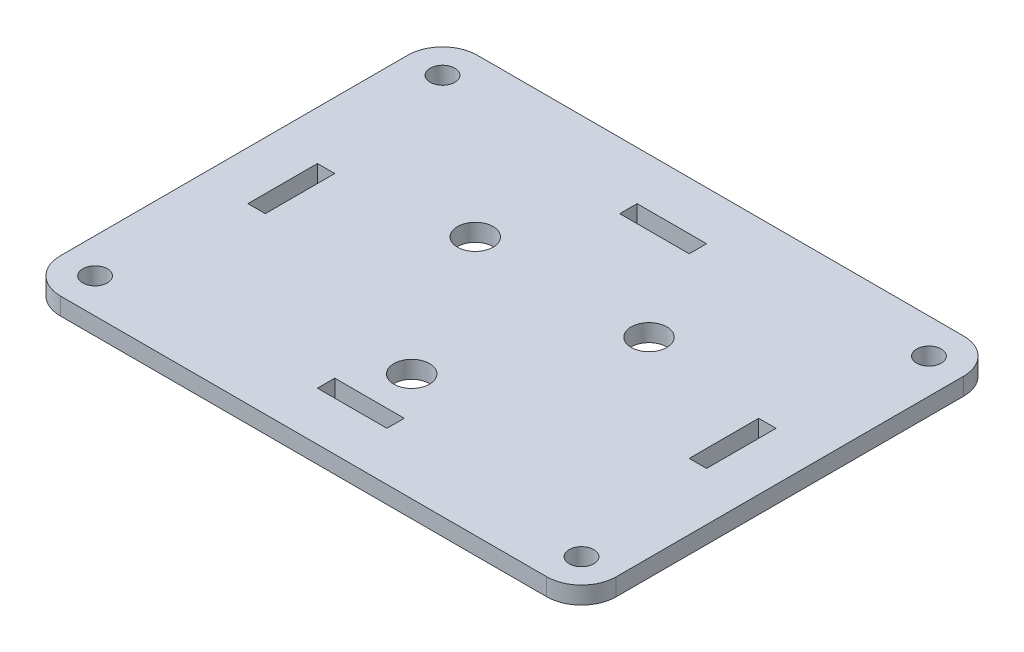
SolidWorks part; units mm, degrees
material "Acrylic (Medium-high impact)"
ref_plane "Front Plane" through (0, 0, 0) normal (0, 0, 1) x (1, 0, 0)
ref_plane "Top Plane" through (0, 0, 0) normal (0, 1, 0) x (1, 0, 0)
ref_plane "Right Plane" through (0, 0, 0) normal (1, 0, 0) x (0, 0, -1)
sketch "Sketch1" plane through (0, 0, 0) normal (0, 1, 0) x (1, 0, 0)
  line L1 (-50.8, -38.1) -> (50.8, -38.1)
  line L2 (-50.8, -38.1) -> (-50.8, 38.1)
  line L3 (-50.8, 38.1) -> (50.8, 38.1)
  line L4 (50.8, -38.1) -> (50.8, 38.1)
  line L5 (-50.8, -38.1) -> (50.8, 38.1) construction
  line L6 (-50.8, 38.1) -> (50.8, -38.1) construction
  point P0 (0, 0)
  dimension "D1" = 101.6
  dimension "D2" = 76.2
extrude "Boss-Extrude1" add sketch "Sketch1" along normal blind 3.175
fillet "Fillet1" radius 6.35 4 edges at (50.8, 1.5875, 38.1) (50.8, 1.5875, -38.1) (-50.8, 1.5875, -38.1) (-50.8, 1.5875, 38.1)
sketch "Sketch2" plane through (0, 3.175, 0) normal (0, 1, 0) x (1, 0, 0)
  line L0 (-50.8, 0) -> (-41.91, 0) construction
  line L1 (-50.8, 31.75) -> (-50.8, -31.75) construction
  line L2 (0, 38.1) -> (0, 29.21) construction
  line L3 (44.45, 38.1) -> (-44.45, 38.1) construction
  line L4 (50.8, 0) -> (41.91, 0) construction
  line L5 (50.8, -31.75) -> (50.8, 31.75) construction
  line L6 (0, -38.1) -> (0, -29.21) construction
  line L7 (-44.45, -38.1) -> (44.45, -38.1) construction
  line L8 (-41.91, 0) -> (-41.91, 6.35)
  line L9 (-41.91, 6.35) -> (-38.735, 6.35)
  line L10 (-38.735, 6.35) -> (-38.735, -6.35)
  line L11 (-38.735, -6.35) -> (-41.91, -6.35)
  line L12 (-41.91, -6.35) -> (-41.91, 0)
  line L13 (0, 29.21) -> (6.35, 29.21)
  line L14 (6.35, 29.21) -> (6.35, 26.035)
  line L15 (6.35, 26.035) -> (-6.35, 26.035)
  line L16 (-6.35, 26.035) -> (-6.35, 29.21)
  line L17 (-6.35, 29.21) -> (0, 29.21)
  line L18 (41.91, 0) -> (41.91, 6.35)
  line L19 (41.91, 6.35) -> (38.735, 6.35)
  line L20 (38.735, 6.35) -> (38.735, -6.35)
  line L21 (38.735, -6.35) -> (41.91, -6.35)
  line L22 (41.91, -6.35) -> (41.91, 0)
  line L23 (0, -29.21) -> (6.35, -29.21)
  line L24 (6.35, -29.21) -> (6.35, -26.035)
  line L25 (6.35, -26.035) -> (-6.35, -26.035)
  line L26 (-6.35, -26.035) -> (-6.35, -29.21)
  line L27 (-6.35, -29.21) -> (0, -29.21)
  circle A0 centre (-44.45, 31.75) radius 2.2479
  circle A1 centre (44.45, 31.75) radius 2.2479
  circle A2 centre (44.45, -31.75) radius 2.2479
  circle A3 centre (-44.45, -31.75) radius 2.2479
  dimension "D1" = 4.4958
  dimension "D2" = 8.89
  dimension "D3" = 3.175
  dimension "D4" = 8.89
  dimension "D5" = 3.175
  dimension "D6" = 12.7
  dimension "D7" = 12.7
extrude "Cut-Extrude1" cut sketch "Sketch2" against normal through all
sketch "Sketch3" plane through (0, 3.175, 0) normal (0, 1, 0) x (1, 0, 0)
  line L0 (0, 0) -> (0, 9.1654) construction
  line L1 (-15.875, 9.1654) -> (15.875, 9.1654) construction
  line L2 (0, 0) -> (-7.9375, -4.5827) construction
  line L3 (-15.875, 9.1654) -> (0, -18.3309) construction
  line L4 (0, -18.3309) -> (15.875, 9.1654) construction
  line L5 (0, 0) -> (7.9375, -4.5827) construction
  circle A0 centre (-15.875, 9.1654) radius 3.2639
  circle A1 centre (15.875, 9.1654) radius 3.2639
  circle A2 centre (0, -18.3309) radius 3.2639
  dimension "D2" = 6.5278
  dimension "D1" = 31.75
extrude "Cut-Extrude2" cut sketch "Sketch3" against normal through all
